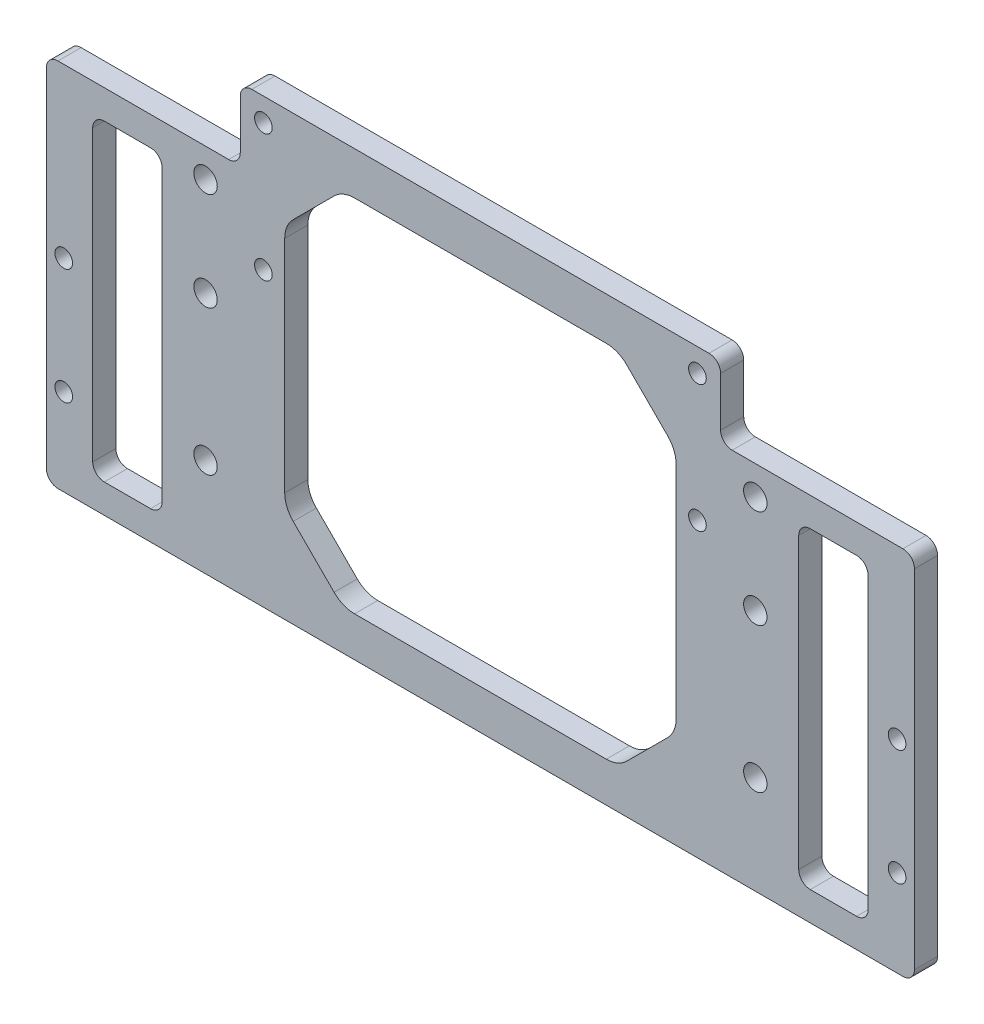
SolidWorks part; units mm, degrees
material "Thornel Mat VMA"
ref_plane "前视基准面" through (0, 0, 0) normal (0, 0, 1) x (1, 0, 0)
ref_plane "上视基准面" through (0, 0, 0) normal (0, 1, 0) x (1, 0, 0)
ref_plane "右视基准面" through (0, 0, 0) normal (1, 0, 0) x (0, 0, -1)
other "Configuration Table"
sketch "草图1" plane through (0, 0, 0) normal (0, 0, 1) x (1, 0, 0)
  line L0 (-47.5, 4) -> (47.5, 4) construction
  line L1 (-47.5, -21) -> (47.5, -21) construction
  line L2 (-47.5, -21) -> (-47.5, 21) construction
  line L3 (-47.5, 21) -> (47.5, 21) construction
  line L4 (47.5, -21) -> (47.5, 21) construction
  line L5 (-47.5, -21) -> (47.5, 21) construction
  line L6 (-47.5, 21) -> (47.5, -21) construction
  line L7 (0, 0) -> (50000, 0) construction
  line L8 (-52.5, -26) -> (52.5, -26)
  line L9 (-52.5, -26) -> (-52.5, 26)
  line L10 (-52.5, 26) -> (52.5, 26)
  line L11 (52.5, -26) -> (52.5, 26)
  line L12 (-52.5, -26) -> (52.5, 26) construction
  line L13 (-52.5, 26) -> (52.5, -26) construction
  line L14 (-39, -22.5) -> (-17, -22.5) construction
  line L15 (-39, -22.5) -> (-39, 22.5) construction
  line L16 (-39, 22.5) -> (-17, 22.5) construction
  line L17 (-17, -22.5) -> (-17, 22.5) construction
  line L18 (-39, -22.5) -> (-17, 22.5) construction
  line L19 (-39, 22.5) -> (-17, -22.5) construction
  line L20 (0, 0) -> (0, -50000) construction
  line L22 (-37.5, 12.5) -> (37.5, 12.5) construction
  line L23 (-37.5, 12.5) -> (-37.5, 34.5) construction
  line L24 (-37.5, 34.5) -> (37.5, 34.5) construction
  line L25 (37.5, 12.5) -> (37.5, 34.5) construction
  line L26 (-37.5, 12.5) -> (37.5, 34.5) construction
  line L27 (-37.5, 34.5) -> (37.5, 12.5) construction
  line L28 (-41.5, 26) -> (41.5, 26)
  line L29 (-41.5, 26) -> (-41.5, 38.5)
  line L30 (-41.5, 38.5) -> (41.5, 38.5)
  line L31 (41.5, 26) -> (41.5, 38.5)
  circle A0 centre (-47.5, 4) radius 2.025
  circle A1 centre (-47.5, 21) radius 2.025
  circle A2 centre (-47.5, -21) radius 2.025
  circle A3 centre (47.5, 21) radius 2.025
  circle A4 centre (47.5, 4) radius 2.025
  circle A5 centre (47.5, -21) radius 2.025
  circle A6 centre (-39, 22.5) radius 1.525 construction
  circle A7 centre (-17, 22.5) radius 1.525 construction
  circle A8 centre (-39, -22.5) radius 1.525 construction
  circle A9 centre (-17, -22.5) radius 1.525 construction
  circle A10 centre (-37.5, 34.5) radius 1.525
  circle A11 centre (-37.5, 12.5) radius 1.525
  circle A12 centre (37.5, 34.5) radius 1.525
  circle A13 centre (37.5, 12.5) radius 1.525
  point P0 (0, 0)
  point P14 (0, 0)
  point P19 (-28, 0)
  point P32 (0, 23.5)
  dimension "D1" = 4.05
  dimension "D2" = 25
  dimension "D3" = 17
  dimension "D9" = 3.05
  dimension "D4" = 95
  dimension "D5" = 5
  dimension "D6" = 5
  dimension "D7" = 22
  dimension "D8" = 45
  dimension "D10" = 28
  dimension "D11" = 75
  dimension "D12" = 22
  dimension "D13" = 12.5
  dimension "D14" = 4
  dimension "D15" = 4
extrude "凸台-拉伸3" add sketch "草图1" along normal blind 4 contours L10 L31 L30 L29 A13 A12 A11 A10 | L8 L11 L10 L9 A9 A8 A7 A6 A5 A4 A3 A2 A1 A0
sketch "草图3" plane through (0, 0, 4) normal (0, 0, 1) x (1, 0, 0)
  line L0 (52.5, -26) -> (52.5, 26) construction
  line L1 (-52.5, 26) -> (-55, 26)
  line L2 (-52.5, 26) -> (-52.5, -38)
  line L3 (-52.5, -38) -> (-55, -38)
  line L4 (-55, 26) -> (-55, -38)
  line L5 (-52.5, -38) -> (52.5, -38)
  line L6 (-52.5, -38) -> (-52.5, -26)
  line L7 (-52.5, -26) -> (52.5, -26)
  line L8 (52.5, -38) -> (52.5, -26)
  line L9 (-52.5, -26) -> (52.5, -26) construction
  line L10 (41.5, 26) -> (52.5, 26) construction
  line L11 (52.5, -38) -> (55, -38)
  line L12 (52.5, -38) -> (52.5, 26)
  line L13 (52.5, 26) -> (55, 26)
  line L14 (55, -38) -> (55, 26)
  line M13 (-52.5, 26) -> (-52.5, -26)
  line M14 (-52.5, -26) -> (52.5, -26)
  line M15 (52.5, -26) -> (52.5, 26)
  dimension "D1" = 2.5
  dimension "D2" = 12
extrude "凸台-拉伸4" add sketch "草图3" against normal up to surface (4 mm away) contours L5 L8 L2 M14 | L1 L4 L3 L2 M13 | L11 L14 L13 L8 M15 up to face at (39.025, 34.5, 0)
sketch "草图4" plane through (0, 0, 4) normal (0, 0, 1) x (1, 0, 0)
  circle A0 centre (-37.5, 34.5) radius 3
  dimension "D1" = 6
sketch "草图5" plane through (0, 0, 0) normal (0, 0, -1) x (-1, 0, 0)
  circle A0 centre (37.5, 34.5) radius 3
  circle A1 centre (37.5, 12.5) radius 3
  circle A2 centre (37.5, 34.5) radius 3 construction
sketch "草图6" plane through (0, 0, 0) normal (0, 0, -1) x (-1, 0, 0)
  line L0 (37.5, 34.5) -> (33.8203, 31.1147) construction
  line L1 (-33.8203, -31.1147) -> (33.8203, -31.1147)
  line L2 (-33.8203, -31.1147) -> (-33.8203, 31.1147)
  line L3 (-33.8203, 31.1147) -> (33.8203, 31.1147)
  line L4 (33.8203, -31.1147) -> (33.8203, 31.1147)
  line L5 (-33.8203, -31.1147) -> (33.8203, 31.1147) construction
  line L6 (-33.8203, 31.1147) -> (33.8203, -31.1147) construction
  circle A0 centre (37.5, 34.5) radius 5
  point P0 (0, 0)
  dimension "D1" = 10
extrude "切除-拉伸1" cut sketch "草图6" against normal blind 4 contours L1 L4 L3 L2
chamfer "倒角1" distance 10 angle 45 4 edges at (-33.8203, -31.1147, 2) (-33.8203, 31.1147, 2) (33.8203, 31.1147, 2) (33.8203, -31.1147, 2)
fillet "圆角2" radius 5 8 edges at (33.8203, 21.1147, 2) (23.8203, 31.1147, 2) (-23.8203, 31.1147, 2) (-33.8203, 21.1147, 2) (-23.8203, -31.1147, 2) (23.8203, -31.1147, 2) (33.8203, -21.1147, 2) (-33.8203, -21.1147, 2)
sketch "草图7" plane through (0, 0, 4) normal (0, 0, 1) x (1, 0, 0)
  line L0 (-72, -3) -> (-72, -23) construction
  line L1 (-55, 26) -> (-75, 26)
  line L2 (-55, 26) -> (-55, -38)
  line L3 (-55, -38) -> (-75, -38)
  line L4 (-75, 26) -> (-75, -38)
  line L5 (55, 26) -> (75, 26)
  line L6 (55, 26) -> (55, -38)
  line L7 (55, -38) -> (75, -38)
  line L8 (75, 26) -> (75, -38)
  line L9 (-72, -23) -> (-72, -38) construction
  line L10 (0, 0) -> (0, -50000) construction
  circle A0 centre (-72, -3) radius 1.525
  circle A1 centre (-72, -23) radius 1.525
  circle A2 centre (72, -23) radius 1.525
  circle A3 centre (72, -3) radius 1.525
  dimension "D5" = 3.05
  dimension "D1" = 20
  dimension "D2" = 20
  dimension "D3" = 15
  dimension "D4" = 3
extrude "凸台-拉伸5" add sketch "草图7" against normal up to surface (4 mm away) up to face at (0, 0, 0)
sketch "草图8" plane through (0, 0, 4) normal (0, 0, 1) x (1, 0, 0)
  line L0 (-75, 26) -> (-41.5, 26) construction
  line L1 (-67, 21) -> (-55, 21)
  line L2 (-67, 21) -> (-67, -33)
  line L3 (-67, -33) -> (-55, -33)
  line L4 (-55, 21) -> (-55, -33)
  line L5 (-75, -38) -> (75, -38) construction
  line L6 (0, 0) -> (0, -50000) construction
  line L7 (67, -33) -> (55, -33)
  line L8 (55, 21) -> (55, -33)
  line L9 (67, 21) -> (55, 21)
  line L10 (67, 21) -> (67, -33)
  circle A0 centre (-72, -3) radius 1.525 construction
  circle A1 centre (-47.5, 21) radius 2.025 construction
  dimension "D1" = 5
  dimension "D2" = 5
  dimension "D3" = 5
  dimension "D4" = 7.5
extrude "切除-拉伸2" cut sketch "草图8" against normal blind 10
fillet "圆角3" radius 2 16 edges at (-41.5, 26, 2) (41.5, 38.5, 2) (41.5, 26, 2) (75, 26, 2) (75, -38, 2) (-75, -38, 2) (-75, 26, 2) (67, 21, 2) (55, 21, 2) (55, -33, 2) (67, -33, 2) (-67, -33, 2) (-55, -33, 2) (-55, 21, 2) (-67, 21, 2) (-41.5, 38.5, 2)
